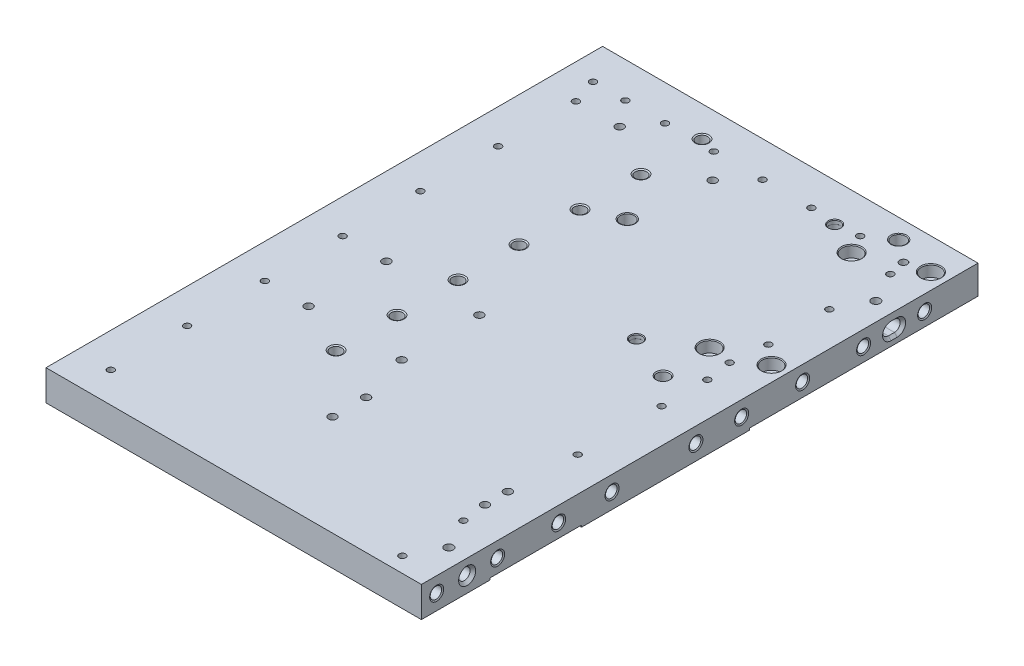
SolidWorks part; units mm, degrees
material "6061-T6 Al"
ref_plane "Front Plane" through (0, 0, 0) normal (0, 0, 1) x (1, 0, 0)
ref_plane "Top Plane" through (0, 0, 0) normal (0, 1, 0) x (1, 0, 0)
ref_plane "Right Plane" through (0, 0, 0) normal (1, 0, 0) x (0, 0, -1)
sketch "Sketch1" plane through (0, 0, 0) normal (0, 1, 0) x (1, 0, 0)
  line L0 (0, 0) -> (0, 231.775) construction
  line L1 (-156.337, 231.775) -> (156.337, 231.775)
  line L2 (-156.337, 231.775) -> (-156.337, -231.775)
  line L3 (-156.337, -231.775) -> (156.337, -231.775)
  line L4 (156.337, 231.775) -> (156.337, -231.775)
  line L5 (0, 0) -> (-156.337, 0) construction
  dimension "D1" = 312.674
  dimension "D2" = 463.55
extrude "Extrude1" add sketch "Sketch1" along normal mid plane 25.4
hole_wizard "3/8-16 Tapped Hole1" positions "Sketch3" profile "Sketch4" tap size "3/8-16" standard "Ansi Inch"
sketch "Sketch3" plane through (-156.337, 0, 0) normal (-1, 0, 0) x (0, 0, 1)
  line L0 (-231.775, 0) -> (231.775, 0) construction
  line L1 (-231.775, 12.7) -> (-231.775, -12.7) construction
  line L2 (231.775, 12.7) -> (231.775, -12.7) construction
  point P1 (-180.975, 0)
  point P3 (-116.205, 0)
  point P5 (-51.435, 0)
  point P7 (13.335, 0)
  point P9 (78.105, 0)
  point P11 (142.875, 0)
  point P13 (206.375, 0)
  dimension "D1" = 50.8
  dimension "D2" = 115.57
  dimension "D3" = 180.34
  dimension "D4" = 245.11
  dimension "D5" = 309.88
  dimension "D6" = 374.65
  dimension "D7" = 438.15
sketch "Sketch4" plane through (-156.337, 0, -180.975) normal (0, 1, 0) x (0, 0, 1)
  line L0 (0, 0) -> (0, 34.1347)
  line L1 (0, 34.1347) -> (3.9687, 31.75)
  line L2 (3.9687, 31.75) -> (3.9687, 25.4)
  line L3 (3.9687, 25.4) -> (4.7625, 25.4)
  line L5 (4.7625, 25.4) -> (4.7625, 0.6232)
  line L6 (4.7625, 0.6232) -> (5.842, 0)
  line L7 (5.842, 0) -> (0, 0)
  line L8 (-4.7625, 0.6232) -> (-5.842, 0) construction
  line L10 (0, 34.1347) -> (-3.9688, 31.75) construction
  line L11 (0, -6.35) -> (0, 107.95) construction
  dimension "Tap Drill Dia." = 7.9375
  dimension "Tap Drill Depth" = 31.75
  dimension "Thread Major Dia." = 9.525
  dimension "Thread Depth" = 25.4
  dimension "Near C'Sink Dia." = 11.684
  dimension "Near C'Sink Angle" = 120
  dimension "Drill Angle" = 118
hole_wizard "7/32 (0.21875) Diameter Hole1" positions "Sketch6" profile "Sketch5" hole size "7/32" standard "Ansi Inch" end condition through all
sketch "Sketch6" plane through (0, -12.7, 0) normal (0, -1, 0) x (1, 0, 0)
  line L0 (-127.762, -231.775) -> (-127.762, 231.775) construction
  line L1 (156.337, -231.775) -> (-156.337, -231.775) construction
  line L2 (-156.337, 231.775) -> (156.337, 231.775) construction
  line L4 (-156.337, -231.775) -> (-156.337, 231.775) construction
  point P0 (-127.762, 13.335)
  point P1 (-127.762, 206.375)
  point P3 (-127.762, 142.875)
  point P5 (-127.762, -180.975)
  point P7 (-127.762, -116.205)
  point P9 (-127.762, -51.435)
  point P11 (-127.762, 78.105)
  dimension "D1" = 28.575
  dimension "D2" = 50.8
  dimension "D3" = 115.57
  dimension "D4" = 180.34
  dimension "D5" = 245.11
  dimension "D6" = 309.88
  dimension "D7" = 374.65
  dimension "D8" = 438.15
sketch "Sketch5" plane through (-127.762, -12.7, 13.335) normal (1, 0, 0) x (0, 0, -1)
  line L0 (0, 0) -> (0, 25.4)
  line L1 (0, 25.4) -> (2.7781, 25.4)
  line L2 (2.7781, 25.4) -> (2.7781, 0)
  line L5 (2.7781, 0) -> (0, 0)
  line L11 (0, -6.35) -> (0, 107.95) construction
  dimension "Thru Hole Dia." = 5.5562
  dimension "Thru Hole Depth" = 25.4
hole_wizard "3/8-16 Tapped Hole2" positions "Sketch8" profile "Sketch7" tap size "3/8-16" standard "Ansi Inch"
sketch "Sketch8" plane through (156.337, 0, 0) normal (1, 0, 0) x (0, 0, -1)
  line L0 (-231.775, 0) -> (231.775, 0) construction
  line L1 (-231.775, 12.7) -> (-231.775, -12.7) construction
  line L2 (231.775, 12.7) -> (231.775, -12.7) construction
  point P0 (136.525, 0)
  point P1 (-219.075, 0)
  point P3 (-168.275, 0)
  point P5 (-117.475, 0)
  point P7 (-73.025, 0)
  point P9 (-3.175, 0)
  point P11 (34.925, 0)
  point P28 (85.725, 0)
  point P30 (187.325, 0)
  dimension "D1" = 12.7
  dimension "D2" = 63.5
  dimension "D3" = 114.3
  dimension "D4" = 158.75
  dimension "D5" = 228.6
  dimension "D6" = 266.7
  dimension "D7" = 368.3
  dimension "D8" = 317.5
  dimension "D9" = 419.1
sketch "Sketch7" plane through (156.337, 0, -136.525) normal (0, 1, 0) x (0, 0, -1)
  line L0 (0, 0) -> (0, 34.1347)
  line L1 (0, 34.1347) -> (3.9687, 31.75)
  line L2 (3.9687, 31.75) -> (3.9687, 25.4)
  line L3 (3.9687, 25.4) -> (4.7625, 25.4)
  line L5 (4.7625, 25.4) -> (4.7625, 0.6232)
  line L6 (4.7625, 0.6232) -> (5.842, 0)
  line L7 (5.842, 0) -> (0, 0)
  line L8 (-4.7625, 0.6232) -> (-5.842, 0) construction
  line L10 (0, 34.1347) -> (-3.9688, 31.75) construction
  line L11 (0, -6.35) -> (0, 107.95) construction
  dimension "Tap Drill Dia." = 7.9375
  dimension "Tap Drill Depth" = 31.75
  dimension "Thread Major Dia." = 9.525
  dimension "Thread Depth" = 25.4
  dimension "Near C'Sink Dia." = 11.684
  dimension "Near C'Sink Angle" = 120
  dimension "Drill Angle" = 118
hole_wizard "7/32 (0.21875) Diameter Hole2" positions "Sketch10" profile "Sketch9" hole size "7/32" standard "Ansi Inch" end condition through all
sketch "Sketch10" plane through (0, -12.7, 0) normal (0, -1, 0) x (1, 0, 0)
  line L0 (127.762, -231.775) -> (127.762, 231.775) construction
  line L1 (156.337, -231.775) -> (-156.337, -231.775) construction
  line L2 (-156.337, 231.775) -> (156.337, 231.775) construction
  line L4 (156.337, 231.775) -> (156.337, -231.775) construction
  point P0 (127.762, -34.925)
  point P14 (127.762, -187.325)
  point P16 (127.762, -136.525)
  point P18 (127.762, -85.725)
  point P20 (127.762, 3.175)
  point P22 (127.762, 73.025)
  point P26 (127.762, 168.275)
  point P28 (127.762, 219.075)
  dimension "D1" = 28.575
  dimension "D3" = 12.7
  dimension "D4" = 63.5
  dimension "D6" = 158.75
  dimension "D7" = 228.6
  dimension "D8" = 266.7
  dimension "D9" = 317.5
  dimension "D10" = 368.3
  dimension "D11" = 419.1
sketch "Sketch9" plane through (127.762, -12.7, -34.925) normal (1, 0, 0) x (0, 0, -1)
  line L0 (0, 0) -> (0, 25.4)
  line L1 (0, 25.4) -> (2.7781, 25.4)
  line L2 (2.7781, 25.4) -> (2.7781, 0)
  line L5 (2.7781, 0) -> (0, 0)
  line L11 (0, -6.35) -> (0, 107.95) construction
  dimension "Thru Hole Dia." = 5.5562
  dimension "Thru Hole Depth" = 25.4
hole_wizard "Tapped Hole for 3/8-16 Helicoil1" positions "Sketch12" profile "Sketch11" tap size "3/8-16" standard "Helicoil® Inch"
sketch "Sketch12" plane through (0, 0, -231.775) normal (0, 0, -1) x (-1, 0, 0)
  line L0 (-156.337, 0) -> (156.337, 0) construction
  line L1 (-156.337, 12.7) -> (-156.337, -12.7) construction
  line L2 (156.337, 12.7) -> (156.337, -12.7) construction
  point P0 (34.163, 0)
  point P10 (-87.757, 0)
  point P12 (-47.117, 0)
  point P14 (-6.477, 0)
  point P16 (74.803, 0)
  point P18 (107.823, 0)
  point P24 (-128.397, 0)
  dimension "D1" = 27.94
  dimension "D3" = 40.64
  dimension "D4" = 40.64
  dimension "D5" = 40.64
  dimension "D6" = 40.64
  dimension "D7" = 40.64
  dimension "D8" = 33.02
sketch "Sketch11" plane through (-34.163, 0, -231.775) normal (1, 0, 0) x (0, 1, 0)
  line L0 (0, 0) -> (0, 36.0495)
  line L1 (0, 36.0495) -> (5.0419, 33.02)
  line L2 (5.0419, 33.02) -> (5.0419, 22.86)
  line L3 (5.0419, 22.86) -> (5.8445, 22.86)
  line L5 (5.8445, 22.86) -> (5.8445, 0.4385)
  line L6 (5.8445, 0.4385) -> (6.604, 0)
  line L7 (6.604, 0) -> (0, 0)
  line L8 (-5.8445, 0.4385) -> (-6.604, 0) construction
  line L10 (0, 36.0495) -> (-5.0419, 33.02) construction
  line L11 (0, -6.35) -> (0, 107.95) construction
  dimension "Tap Drill Dia." = 10.0838
  dimension "Tap Drill Depth" = 33.02
  dimension "Thread Major Dia." = 11.6891
  dimension "Thread Depth" = 22.86
  dimension "Near C'Sink Dia." = 13.208
  dimension "Near C'Sink Angle" = 120
  dimension "Drill Angle" = 118
hole_wizard "7/32 (0.21875) Diameter Hole3" positions "Sketch14" profile "Sketch13" hole size "7/32" standard "Ansi Inch" end condition through all
sketch "Sketch14" plane through (0, -12.7, 0) normal (0, -1, 0) x (1, 0, 0)
  line L0 (-156.337, -202.2094) -> (156.337, -202.2094) construction
  line L1 (-156.337, -231.775) -> (-156.337, 231.775) construction
  line L2 (156.337, 231.775) -> (156.337, -231.775) construction
  line L4 (156.337, -231.775) -> (-156.337, -231.775) construction
  point P0 (6.477, -202.2094)
  point P14 (-107.823, -202.2094)
  point P16 (-74.803, -202.2094)
  point P20 (-34.163, -202.2094)
  point P22 (47.117, -202.2094)
  point P24 (87.757, -202.2094)
  point P25 (-134.747, -202.2094)
  dimension "D1" = 29.5656
  dimension "D2" = 33.02
  dimension "D3" = 68.58
  dimension "D4" = 40.64
  dimension "D5" = 40.64
  dimension "D6" = 40.64
  dimension "D7" = 40.64
  dimension "D8" = 291.084
sketch "Sketch13" plane through (6.477, -12.7, -202.2094) normal (1, 0, 0) x (0, 0, -1)
  line L0 (0, 0) -> (0, 25.4)
  line L1 (0, 25.4) -> (2.7781, 25.4)
  line L2 (2.7781, 25.4) -> (2.7781, 0)
  line L5 (2.7781, 0) -> (0, 0)
  line L11 (0, -6.35) -> (0, 107.95) construction
  dimension "Thru Hole Dia." = 5.5562
  dimension "Thru Hole Depth" = 25.4
sketch "Sketch15" plane through (156.337, 0, 0) normal (1, 0, 0) x (0, 0, -1)
  line L0 (159.385, 0) -> (164.465, 0) construction
  line L1 (159.385, 4.7714) -> (164.465, 4.7714)
  line L2 (159.385, -4.7714) -> (164.465, -4.7714)
  line L3 (231.775, 12.7) -> (231.775, -12.7) construction
  arc A1 (159.385, 4.7714) -> (159.385, -4.7714) centre (159.385, 0) ccw
  arc A2 (164.465, -4.7714) -> (164.465, 4.7714) centre (164.465, 0) ccw
  point P0 (231.775, 0)
  point P5 (161.925, 0)
  dimension "D1" = 69.85
  dimension "D2" = 4.7714
  dimension "D3" = 5.08
extrude "Extrude2" cut sketch "Sketch15" against normal blind 19.05
hole_wizard "3/8 (0.375) Diameter Hole1" positions "Sketch17" profile "Sketch16" hole size "3/8" standard "Ansi Inch"
sketch "Sketch17" plane through (156.337, 0, 0) normal (1, 0, 0) x (0, 0, -1)
  line L0 (-231.775, 12.7) -> (231.775, 12.7) construction
  line L1 (-231.775, 12.7) -> (-231.775, -12.7) construction
  point P0 (-193.675, 0)
  dimension "D1" = 12.7
  dimension "D2" = 38.1
sketch "Sketch16" plane through (156.337, 0, 193.675) normal (0, 1, 0) x (0, 0, -1)
  line L0 (0, 0) -> (0, 21.9169)
  line L1 (0, 21.9169) -> (4.7714, 19.05)
  line L2 (4.7714, 19.05) -> (4.7714, 2.3406)
  line L3 (4.7714, 2.3406) -> (7.112, 0)
  line L5 (7.112, 0) -> (0, 0)
  line L6 (-4.7714, 2.3406) -> (-7.112, 0) construction
  line L10 (0, 21.9169) -> (-4.7714, 19.05) construction
  line L11 (0, -6.35) -> (0, 107.95) construction
  dimension "Hole Dia." = 9.5428
  dimension "Hole Depth" = 19.05
  dimension "Near C'Sink Dia." = 14.224
  dimension "Near C'Sink Angle" = 90
  dimension "Drill Angle" = 118
chamfer "Chamfer1" distance 2.286 angle 45 4 edges at (156.337, 0, -169.2364) (156.337, 4.7714, -161.925) (156.337, -4.7714, -161.925) (156.337, 0, -154.6136)
hole_wizard "CBORE for 3/8 Socket Head Cap Screw1" positions "Sketch19" profile "Sketch18" counterbore size "3/8" standard "Ansi Inch" end condition through all
sketch "Sketch19" plane through (0, 12.7, 0) normal (0, 1, 0) x (-1, 0, 0)
  line L0 (-156.337, -231.775) -> (156.337, -231.775) construction
  line L1 (-156.337, 231.775) -> (-156.337, -231.775) construction
  point P0 (-96.139, -186.69)
  point P3 (-105.537, -59.055)
  point P6 (-143.764, -72.39)
  point P9 (-143.129, -205.74)
  dimension "D1" = 26.035
  dimension "D2" = 45.085
  dimension "D3" = 13.208
  dimension "D4" = 60.198
  dimension "D5" = 12.573
  dimension "D6" = 50.8
  dimension "D7" = 159.385
  dimension "D8" = 172.72
sketch "Sketch18" plane through (96.139, 12.7, -186.69) normal (1, 0, 0) x (0, 0, 1)
  line L0 (0, 0) -> (0, 25.4)
  line L1 (0, 25.4) -> (4.9022, 25.4)
  line L3 (4.9022, 25.4) -> (4.9022, 9.525)
  line L4 (7.9375, 9.525) -> (4.9022, 9.525)
  line L5 (7.9375, 9.525) -> (7.9375, 0.635)
  line L6 (7.9375, 0.635) -> (8.5725, 0)
  line L7 (8.5725, 0) -> (0, 0)
  line L8 (-7.9375, 0.635) -> (-8.5725, 0) construction
  line L11 (0, -6.35) -> (0, 107.95) construction
  dimension "Thru Hole Dia." = 9.8044
  dimension "Thru Hole Depth" = 25.4
  dimension "C'Bore Dia." = 15.875
  dimension "C'Bore Depth" = 9.525
  dimension "Near C'Sink Dia." = 17.145
  dimension "Near C'Sink Angle" = 90
sketch "Sketch20" plane through (0, -12.7, 0) normal (0, -1, 0) x (1, 0, 0)
  line L1 (156.337, -231.775) -> (54.737, -231.775)
  line L2 (156.337, -231.775) -> (156.337, -41.275)
  line L3 (156.337, -41.275) -> (54.737, -41.275)
  line L4 (54.737, -231.775) -> (54.737, -41.275)
  dimension "D1" = 101.6
  dimension "D2" = 190.5
extrude "Cut-Extrude1" cut sketch "Sketch20" against normal blind 1.524
fillet "Fillet1" radius 12.7 1 edges at (54.737, -11.938, -41.275)
sketch "Sketch21" plane through (0, -11.176, 0) normal (0, -1, 0) x (1, 0, 0)
  line L0 (124.714, -58.166) -> (124.714, -54.864) construction
  line L1 (121.5301, -58.166) -> (121.5301, -54.864)
  line L2 (127.8979, -58.166) -> (127.8979, -54.864)
  line L5 (156.337, -231.775) -> (156.337, -41.275) construction
  line L6 (54.737, -231.775) -> (156.337, -231.775) construction
  arc A1 (121.5301, -58.166) -> (127.8979, -58.166) centre (124.714, -58.166) ccw
  arc A2 (127.8979, -54.864) -> (121.5301, -54.864) centre (124.714, -54.864) ccw
  point P5 (124.714, -56.515)
  dimension "D1" = 31.623
  dimension "D3" = 175.26
  dimension "D4" = 3.1839
  dimension "D2" = 3.302
extrude "Cut-Extrude2" cut sketch "Sketch21" against normal blind 9.652
chamfer "Chamfer2" distance 1.524 angle 45 4 edges at (127.8979, -11.176, -56.515) (124.714, -11.176, -51.6801) (124.714, -11.176, -61.3499) (121.5301, -11.176, -56.515)
hole_wizard "1/4 DOWEL HOLE" positions "Sketch45" profile "Sketch44" hole size "1/4" standard "Ansi Inch" end condition through all
sketch "Sketch45" plane through (0, -11.176, 0) normal (0, -1, 0) x (1, 0, 0)
  line L0 (54.737, -231.775) -> (156.337, -231.775) construction
  line L3 (124.714, -58.166) -> (124.714, -201.295) construction
  point P0 (124.714, -201.295)
  dimension "D1" = 30.48
sketch "Sketch44" plane through (124.714, -11.176, -201.295) normal (1, 0, 0) x (0, 0, -1)
  line L0 (0, 0) -> (0, 23.876)
  line L1 (0, 23.876) -> (3.1839, 23.876)
  line L2 (3.1839, 23.876) -> (3.1839, 1.6421)
  line L3 (3.1839, 1.6421) -> (4.826, 0)
  line L5 (4.826, 0) -> (0, 0)
  line L6 (-3.1839, 1.6421) -> (-4.826, 0) construction
  line L11 (0, -6.35) -> (0, 107.95) construction
  dimension "Thru Hole Dia." = 6.3678
  dimension "Thru Hole Depth" = 23.876
  dimension "Near C'Sink Dia." = 9.652
  dimension "Near C'Sink Angle" = 90
hole_wizard "7/32 (0.21875) Diameter Hole5" positions "Sketch23" profile "Sketch22" hole size "7/32" standard "Ansi Inch" end condition up to next
sketch "Sketch23" plane through (0, 12.7, 0) normal (0, 1, 0) x (-1, 0, 0)
  line L0 (-156.337, 231.775) -> (-156.337, -231.775) construction
  line L1 (-156.337, -231.775) -> (156.337, -231.775) construction
  line L2 (-124.714, -56.515) -> (-124.714, -205.74) construction
  point P4 (-124.714, -56.515)
  dimension "D1" = 31.623
  dimension "D2" = 175.26
sketch "Sketch22" plane through (124.714, 12.7, -56.515) normal (1, 0, 0) x (0, 0, 1)
  line L0 (0, 0) -> (0, 14.224)
  line L1 (0, 14.224) -> (2.7781, 14.224)
  line L2 (2.7781, 14.224) -> (2.7781, 0)
  line L5 (2.7781, 0) -> (0, 0)
  line L11 (0, -6.35) -> (0, 107.95) construction
  dimension "Thru Hole Dia." = 5.5562
  dimension "Thru Hole Depth" = 14.224
sketch "Sketch24" plane through (0, -12.7, 0) normal (0, -1, 0) x (1, 0, 0)
  line L1 (-15.113, 98.425) -> (156.337, 98.425)
  line L2 (-27.813, 111.125) -> (-27.813, 161.925)
  line L3 (-15.113, 174.625) -> (156.337, 174.625)
  line L4 (156.337, 98.425) -> (156.337, 174.625)
  line L5 (-156.337, 231.775) -> (156.337, 231.775) construction
  line L6 (156.337, 231.775) -> (156.337, -41.275) construction
  arc A0 (-15.113, 98.425) -> (-27.813, 111.125) centre (-15.113, 111.125) cw
  arc A1 (-15.113, 174.625) -> (-27.813, 161.925) centre (-15.113, 161.925) ccw
  dimension "D5" = 12.7
  dimension "D1" = 76.2
  dimension "D2" = 184.15
  dimension "D4" = 57.15
extrude "Cut-Extrude3" cut sketch "Sketch24" against normal blind 1.524
hole_wizard "Tapped Hole for 1/4-20 Helicoil2" positions "Sketch49" profile "Sketch50" tap size "1/4-20" standard "Helicoil® Inch" end condition through all
sketch "Sketch49" plane through (0, -12.7, 0) normal (0, -1, 0) x (1, 0, 0)
  line L0 (-91.313, -180.975) -> (-13.843, -180.975) construction
  line L1 (-91.313, -180.975) -> (-91.313, 13.335) construction
  line L2 (-91.313, 13.335) -> (-91.313, 78.105) construction
  line L3 (-91.313, 78.105) -> (-13.843, 78.105) construction
  line L4 (-91.313, 13.335) -> (-13.843, 13.335) construction
  line L5 (-13.843, 78.105) -> (-13.843, 13.335) construction
  line L6 (-13.843, 13.335) -> (-13.843, -180.975) construction
  line L7 (-127.762, -180.975) -> (-91.313, -180.975) construction
  line L8 (-127.762, 78.105) -> (-91.313, 78.105) construction
  line L9 (-127.762, 13.335) -> (-91.313, 13.335) construction
  line L10 (-156.337, -231.775) -> (-156.337, 231.775) construction
  point P0 (-91.313, -180.975)
  point P1 (-91.313, 13.335)
  point P3 (-91.313, 78.105)
  point P5 (-13.843, 78.105)
  point P7 (-13.843, 13.335)
  point P9 (-13.843, -180.975)
  dimension "D1" = 65.024
  dimension "D2" = 77.47
sketch "Sketch50" plane through (-91.313, -12.7, -180.975) normal (1, 0, 0) x (0, 0, -1)
  line L0 (0, 0) -> (0, 25.4)
  line L1 (0, 25.4) -> (3.3782, 25.4)
  line L3 (3.3782, 25.4) -> (3.3782, 15.748)
  line L4 (4.0475, 15.748) -> (3.3782, 15.748)
  line L5 (4.0475, 15.748) -> (4.0475, 0.3666)
  line L6 (4.0475, 0.3666) -> (4.6825, 0)
  line L7 (4.6825, 0) -> (0, 0)
  line L8 (-4.0475, 0.3666) -> (-4.6825, 0) construction
  line L11 (0, -6.35) -> (0, 107.95) construction
  dimension "Thru Tap Drill Dia." = 6.7564
  dimension "Thru Tap Drill Depth" = 25.4
  dimension "Thread Major Dia." = 8.095
  dimension "Thread Depth" = 15.748
  dimension "Near C'Sink Dia." = 9.365
  dimension "Near C'Sink Angle" = 120
hole_wizard "Tapped Hole for 1/4-20 Helicoil1" positions "Sketch27" profile "Sketch26" tap size "1/4-20" standard "Helicoil® Inch" end condition through all
sketch "Sketch27" plane through (-51.6142, -11.176, -90.4519) normal (0, -1, 0) x (1, 0, 0)
  line L11 (207.9512, 238.2799) -> (49.9632, 238.2799) construction
  line L12 (207.9512, 322.2269) -> (207.9512, -141.3231) construction
  line L13 (49.9632, 238.2799) -> (49.9632, 210.3399) construction
  line L16 (-104.7228, 322.2269) -> (207.9512, 322.2269) construction
  line L17 (176.9632, 238.2799) -> (176.9632, 219.2299) construction
  point P0 (176.9632, 219.2299)
  point P2 (176.9632, 238.2799)
  point P52 (49.9632, 210.3399)
  point P54 (49.9632, 238.2799)
  dimension "D1" = 83.947
  dimension "D2" = 27.94
  dimension "D3" = 157.988
  dimension "D4" = 30.988
  dimension "D5" = 19.05
sketch "Sketch26" plane through (125.349, -11.176, 128.778) normal (1, 0, 0) x (0, 0, -1)
  line L0 (0, 0) -> (0, 23.876)
  line L1 (0, 23.876) -> (3.3782, 23.876)
  line L3 (3.3782, 23.876) -> (3.3782, 15.748)
  line L4 (4.0475, 15.748) -> (3.3782, 15.748)
  line L5 (4.0475, 15.748) -> (4.0475, 0.3028)
  line L6 (4.0475, 0.3028) -> (4.572, 0)
  line L7 (4.572, 0) -> (0, 0)
  line L8 (-4.0475, 0.3028) -> (-4.572, 0) construction
  line L11 (0, -6.35) -> (0, 107.95) construction
  dimension "Thru Tap Drill Dia." = 6.7564
  dimension "Thru Tap Drill Depth" = 23.876
  dimension "Thread Major Dia." = 8.095
  dimension "Thread Depth" = 15.748
  dimension "Near C'Sink Dia." = 9.144
  dimension "Near C'Sink Angle" = 120
hole_wizard "L4C Holes Tapped Hole for 3/8-16 Helicoil2" positions "Sketch29" profile "Sketch28" tap size "3/8-16" standard "Helicoil® Inch" end condition through all
sketch "Sketch29" plane through (0, 12.7, 0) normal (0, 1, 0) x (-1, 0, 0)
  line L0 (-80.137, -117.475) -> (21.463, -117.475) construction
  line L2 (-80.137, -117.475) -> (-106.433, -19.3369) construction
  line L4 (-80.137, -117.475) -> (-106.433, -215.6131) construction
  line L8 (-156.337, -231.775) -> (156.337, -231.775) construction
  line L9 (-156.337, 231.775) -> (-156.337, -231.775) construction
  point P0 (21.463, -117.475)
  point P19 (-106.433, -215.6131)
  dimension "D1" = 101.6
  dimension "D2" = 101.6
  dimension "D3" = 101.6
  dimension "D4" = 105
  dimension "D5" = 105
  dimension "D6" = 114.3
  dimension "D7" = 76.2
sketch "Sketch28" plane through (-21.463, 12.7, -117.475) normal (1, 0, 0) x (0, 0, 1)
  line L0 (0, 0) -> (0, 25.4)
  line L1 (0, 25.4) -> (5.0419, 25.4)
  line L3 (5.0419, 25.4) -> (5.0419, 22.86)
  line L4 (5.8445, 22.86) -> (5.0419, 22.86)
  line L5 (5.8445, 22.86) -> (5.8445, 0.4385)
  line L6 (5.8445, 0.4385) -> (6.604, 0)
  line L7 (6.604, 0) -> (0, 0)
  line L8 (-5.8445, 0.4385) -> (-6.604, 0) construction
  line L11 (0, -6.35) -> (0, 107.95) construction
  dimension "Thru Tap Drill Dia." = 10.0838
  dimension "Thru Tap Drill Depth" = 25.4
  dimension "Thread Major Dia." = 11.6891
  dimension "Thread Depth" = 22.86
  dimension "Near C'Sink Dia." = 13.208
  dimension "Near C'Sink Angle" = 120
hole_wizard "Holes for Pins 3/8 Clearance Hole1" positions "Sketch31" profile "Sketch30" counterbore size "3/8" standard "Ansi Inch"
sketch "Sketch31" plane through (0, 12.7, 0) normal (0, 1, 0) x (-1, 0, 0)
  line L0 (-68.707, -34.925) -> (-68.707, -200.025) construction
  line L2 (-156.337, 231.775) -> (-156.337, -231.775) construction
  line L3 (21.463, -117.475) -> (-68.707, -117.475) construction
  line L5 (-156.337, -231.775) -> (156.337, -231.775) construction
  point P0 (-68.707, -34.925)
  point P1 (-68.707, -200.025)
  dimension "D1" = 87.63
  dimension "D2" = 165.1
sketch "Sketch30" plane through (68.707, 12.7, -34.925) normal (1, 0, 0) x (0, 0, 1)
  line L0 (0, 0) -> (0, 20.0025)
  line L1 (0, 20.0025) -> (4.7625, 15.24)
  line L2 (4.7625, 15.24) -> (4.7625, 3.302)
  line L3 (4.7625, 3.302) -> (4.7879, 3.302)
  line L5 (4.7879, 3.302) -> (4.7879, 0.5461)
  line L6 (4.7879, 0.5461) -> (5.334, 0)
  line L7 (5.334, 0) -> (0, 0)
  line L8 (-4.7879, 0.5461) -> (-5.334, 0) construction
  line L10 (0, 20.0025) -> (-4.7625, 15.24) construction
  line L11 (0, -6.35) -> (0, 107.95) construction
  dimension "Hole Dia." = 9.525
  dimension "Hole Depth" = 15.24
  dimension "C'Bore Dia." = 9.5758
  dimension "C'Bore Depth" = 3.302
  dimension "Near C'Sink Dia." = 10.668
  dimension "Near C'Sink Angle" = 90
  dimension "Drill Angle" = 90
hole_wizard "Vent Holes for Pins 7/32 (0.21875) Diameter Hole4" positions "Sketch33" profile "Sketch32" hole size "9/32" standard "Ansi Inch" end condition through all
sketch "Sketch33" plane through (-225.044, 12.7, 349.25) normal (0, 1, 0) x (-1, 0, 0)
  point P16 (-293.751, -384.175)
  point P19 (-293.751, -549.275)
sketch "Sketch32" plane through (68.707, 12.7, -34.925) normal (1, 0, 0) x (0, 0, 1)
  line L0 (0, 0) -> (0, 25.4)
  line L1 (0, 25.4) -> (3.5719, 25.4)
  line L2 (3.5719, 25.4) -> (3.5719, 0)
  line L5 (3.5719, 0) -> (0, 0)
  line L11 (0, -6.35) -> (0, 107.95) construction
  dimension "Thru Hole Dia." = 7.1437
  dimension "Thru Hole Depth" = 25.4
hole_wizard "3/8-16 Tapped Hole3" positions "Sketch35" profile "Sketch34" tap size "3/8-16" standard "Ansi Inch" end condition through all
sketch "Sketch35" plane through (0, 12.7, 0) normal (0, 1, 0) x (-1, 0, 0)
  line L0 (48.133, 231.775) -> (48.133, -231.775) construction
  line L1 (156.337, 231.775) -> (-156.337, 231.775) construction
  line L2 (-156.337, -231.775) -> (156.337, -231.775) construction
  line L4 (156.337, -231.775) -> (156.337, 231.775) construction
  point P13 (48.133, -206.375)
  point P15 (48.133, -155.575)
  point P17 (48.133, -104.775)
  point P19 (48.133, -53.975)
  point P21 (48.133, -3.175)
  point P23 (48.133, 47.625)
  point P25 (48.133, 98.425)
  dimension "D1" = 108.204
  dimension "D2" = 25.4
  dimension "D3" = 76.2
  dimension "D4" = 127
  dimension "D5" = 177.8
  dimension "D6" = 228.6
  dimension "D7" = 279.4
  dimension "D8" = 330.2
sketch "Sketch34" plane through (-48.133, 12.7, -206.375) normal (1, 0, 0) x (0, 0, 1)
  line L0 (0, 0) -> (0, 25.4)
  line L1 (0, 25.4) -> (4.7625, 25.4)
  line L2 (4.7625, 25.4) -> (4.7625, 0.6232)
  line L3 (4.7625, 0.6232) -> (5.842, 0)
  line L5 (5.842, 0) -> (0, 0)
  line L6 (-4.7625, 0.6232) -> (-5.842, 0) construction
  line L11 (0, -6.35) -> (0, 107.95) construction
  dimension "Thread Major Dia." = 9.525
  dimension "Thru Tap Drill Depth" = 25.4
  dimension "Near C'Sink Dia." = 11.684
  dimension "Near C'Sink Angle" = 120
hole_wizard "9/32 (0.28125) Diameter Hole1" positions "Sketch37" profile "Sketch36" hole size "9/32" standard "Ansi Inch" end condition through all
sketch "Sketch37" plane through (0, -12.7, 0) normal (0, -1, 0) x (1, 0, 0)
  line L0 (141.097, 231.775) -> (141.097, -231.7732) construction
  line L1 (-156.337, 231.775) -> (156.337, 231.775) construction
  line L3 (156.337, -231.775) -> (156.337, -41.275) construction
  line L4 (54.737, -231.775) -> (156.337, -231.775) construction
  point P0 (141.097, 193.675)
  point P1 (141.097, -161.925)
  dimension "D1" = 15.24
  dimension "D2" = 69.85
  dimension "D3" = 38.1
sketch "Sketch36" plane through (141.097, -12.7, 193.675) normal (1, 0, 0) x (0, 0, -1)
  line L0 (0, 0) -> (0, 25.4)
  line L1 (0, 25.4) -> (3.5719, 25.4)
  line L2 (3.5719, 25.4) -> (3.5719, 0)
  line L5 (3.5719, 0) -> (0, 0)
  line L11 (0, -6.35) -> (0, 107.95) construction
  dimension "Thru Hole Dia." = 7.1437
  dimension "Thru Hole Depth" = 25.4
hole_wizard "CBORE for 3/8 Socket Head Cap Screw2" positions "Sketch39" profile "Sketch38" counterbore size "3/8" standard "Ansi Inch" end condition through all
sketch "Sketch39" plane through (0, -12.7, 0) normal (0, -1, 0) x (1, 0, 0)
  point P0 (106.433, -19.3369)
sketch "Sketch38" plane through (106.433, -12.7, -19.3369) normal (1, 0, 0) x (0, 0, -1)
  line L0 (0, 0) -> (0, 25.4)
  line L1 (5.1587, 24.614) -> (5.842, 25.4)
  line L2 (5.1587, 24.614) -> (5.1587, 12.7)
  line L3 (5.1587, 12.7) -> (8.7376, 12.7)
  line L4 (8.7376, 12.7) -> (8.7376, 0)
  line L5 (8.7376, 0) -> (0, 0)
  line L11 (0, -6.35) -> (0, 107.95) construction
  line L12 (5.842, 25.4) -> (0, 25.4)
  line L13 (-5.1587, 24.614) -> (-5.842, 25.4) construction
  dimension "Thru Hole Dia." = 10.3175
  dimension "Thru Hole Depth" = 25.4
  dimension "C'Bore Dia." = 17.4752
  dimension "C'Bore Depth" = 12.7
  dimension "Far C'Sink Dia." = 11.684
  dimension "Far C'Sink Angle" = 82
hole_wizard "CBORE for 3/8 Socket Head Cap Screw3" positions "Sketch41" profile "Sketch40" counterbore size "3/8" standard "Ansi Inch"
sketch "Sketch41" plane through (-156.337, 0, 0) normal (-1, 0, 0) x (0, 0, 1)
  line L0 (-231.775, 12.7) -> (-231.775, -12.7) construction
  line L1 (-231.775, -12.7) -> (231.775, -12.7) construction
  point P0 (-202.2148, 0)
  dimension "D1" = 29.5602
  dimension "D2" = 12.7
sketch "Sketch40" plane through (-156.337, 0, -202.2148) normal (0, 1, 0) x (0, 0, 1)
  line L0 (0, 0) -> (0, 18.1016)
  line L1 (0, 18.1016) -> (4.7625, 15.24)
  line L2 (4.7625, 15.24) -> (4.7625, 3.302)
  line L3 (4.7625, 3.302) -> (4.7879, 3.302)
  line L5 (4.7879, 3.302) -> (4.7879, 0.5461)
  line L6 (4.7879, 0.5461) -> (5.334, 0)
  line L7 (5.334, 0) -> (0, 0)
  line L8 (-4.7879, 0.5461) -> (-5.334, 0) construction
  line L10 (0, 18.1016) -> (-4.7625, 15.24) construction
  line L11 (0, -6.35) -> (0, 107.95) construction
  dimension "Hole Dia." = 9.525
  dimension "Hole Depth" = 15.24
  dimension "C'Bore Dia." = 9.5758
  dimension "C'Bore Depth" = 3.302
  dimension "Near C'Sink Dia." = 10.668
  dimension "Near C'Sink Angle" = 90
  dimension "Drill Angle" = 118
hole_wizard "9/32 (0.28125) Diameter Hole2" positions "Sketch47" profile "Sketch46" hole size "9/32" standard "Ansi Inch"
sketch "Sketch47" plane through (-156.337, 0, 0) normal (-1, 0, 0) x (0, 0, 1)
  circle A0 centre (-202.2148, 0) radius 5.334 construction
  point P0 (-202.2148, 0)
sketch "Sketch46" plane through (-156.337, 0, -202.2148) normal (0, 1, 0) x (0, 0, 1)
  line L0 (0, 0) -> (0, 27.2331)
  line L1 (0, 27.2331) -> (3.175, 25.4)
  line L2 (3.175, 25.4) -> (3.175, 0)
  line L5 (3.175, 0) -> (0, 0)
  line L10 (0, 27.2331) -> (-3.175, 25.4) construction
  line L11 (0, -6.35) -> (0, 107.95) construction
  dimension "Hole Dia." = 6.35
  dimension "Hole Depth" = 25.4
  dimension "Drill Angle" = 120
